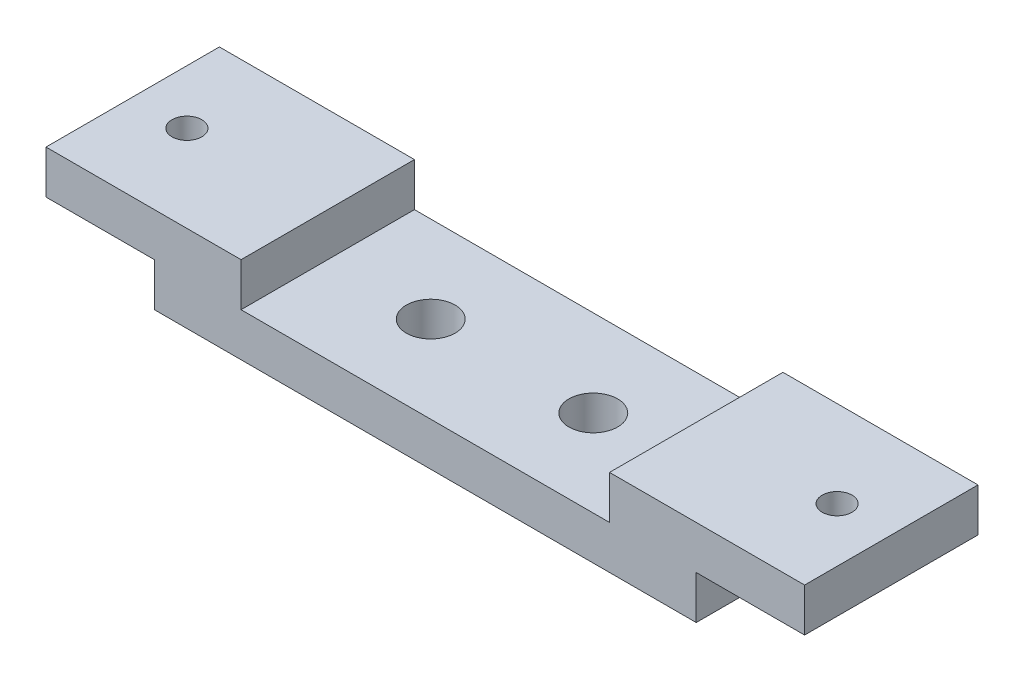
SolidWorks part; units mm, degrees
ref_plane "Ebene vorne" through (0, 0, 0) normal (0, 0, 1) x (1, 0, 0)
ref_plane "Ebene oben" through (0, 0, 0) normal (0, 1, 0) x (1, 0, 0)
ref_plane "Ebene rechts" through (0, 0, 0) normal (1, 0, 0) x (0, 0, -1)
sketch "Skizze1" plane through (0, 0, 0) normal (0, 0, 1) x (1, 0, 0)
  line L0 (-70, 16) -> (-34, 16)
  line L1 (-34, 8) -> (34, 8)
  line L2 (34, 8) -> (34, 16)
  line L3 (34, 16) -> (70, 16)
  line L4 (70, 16) -> (70, 8)
  line L5 (70, 8) -> (50, 8)
  line L7 (-50, 8) -> (-70, 8)
  line L8 (-70, 8) -> (-70, 16)
  line L9 (-34, 16) -> (-34, 8)
  line L10 (-50, 8) -> (-50, 0)
  line L11 (-50, 0) -> (50, 0)
  line L12 (50, 0) -> (50, 8)
  point P12 (0, 0)
  point P13 (34, 12)
  point P15 (0, 8)
  dimension "D1" = 8
  dimension "D2" = 68
  dimension "D3" = 68
  dimension "D4" = 8
  dimension "D5" = 8
  dimension "D6" = 16
  dimension "D7" = 20
extrude "Aufsatz-Linear austragen1" add sketch "Skizze1" along normal blind 32
hole_wizard "Ø9.0 (9) Durchmesser Bohrung1" positions "3D-Skizze4" profile "Skizze5" hole size "Ø9.0" standard "ANSI Metrisch" end condition through all
sketch3d "3D-Skizze4"
  line L5 (-34, 8, 16) -> (34, 8, 16) construction
  line L6 (-34, 8, 32) -> (-34, 8, 0) construction
  line L7 (34, 8, 32) -> (34, 8, 0) construction
  point P0 (15, 8, 16)
  point P2 (-15, 8, 16)
  point P47 (-15, 8, 16)
  point P49 (15, 8, 16)
  dimension "D1" = 30
  dimension "D2" = 19
sketch "Skizze5" plane through (15, 8, 16) normal (1, 0, 0) x (0, 0, 1)
  line L0 (0, 0) -> (0, 8)
  line L1 (0, 8) -> (4.5, 8)
  line L2 (4.5, 8) -> (4.5, 0)
  line L5 (4.5, 0) -> (0, 0)
  line L11 (0, -6.35) -> (0, 107.95) construction
  dimension "Bohrerdurchmesser" = 9
  dimension "Bohrungstiefe" = 8
hole_wizard "Ø5.5 (5.5) Durchmesser Bohrung1" positions "3D-Skizze5" profile "Skizze6" hole size "Ø5.5" standard "ANSI Metrisch" end condition through all
sketch3d "3D-Skizze5"
  line L0 (50, 8, 0) -> (70, 8, 32) construction
  line L2 (70, 8, 0) -> (50, 8, 32) construction
  line L4 (-70, 8, 0) -> (-50, 8, 32) construction
  line L6 (-50, 8, 0) -> (-70, 8, 32) construction
  point P0 (-60, 8, 16)
  point P2 (60, 8, 16)
sketch "Skizze6" plane through (-60, 8, 16) normal (1, 0, 0) x (0, 0, -1)
  line L0 (0, 0) -> (0, 8)
  line L1 (0, 8) -> (2.75, 8)
  line L2 (2.75, 8) -> (2.75, 0)
  line L5 (2.75, 0) -> (0, 0)
  line L11 (0, -6.35) -> (0, 107.95) construction
  dimension "Bohrerdurchmesser" = 5.5
  dimension "Bohrungstiefe" = 8
